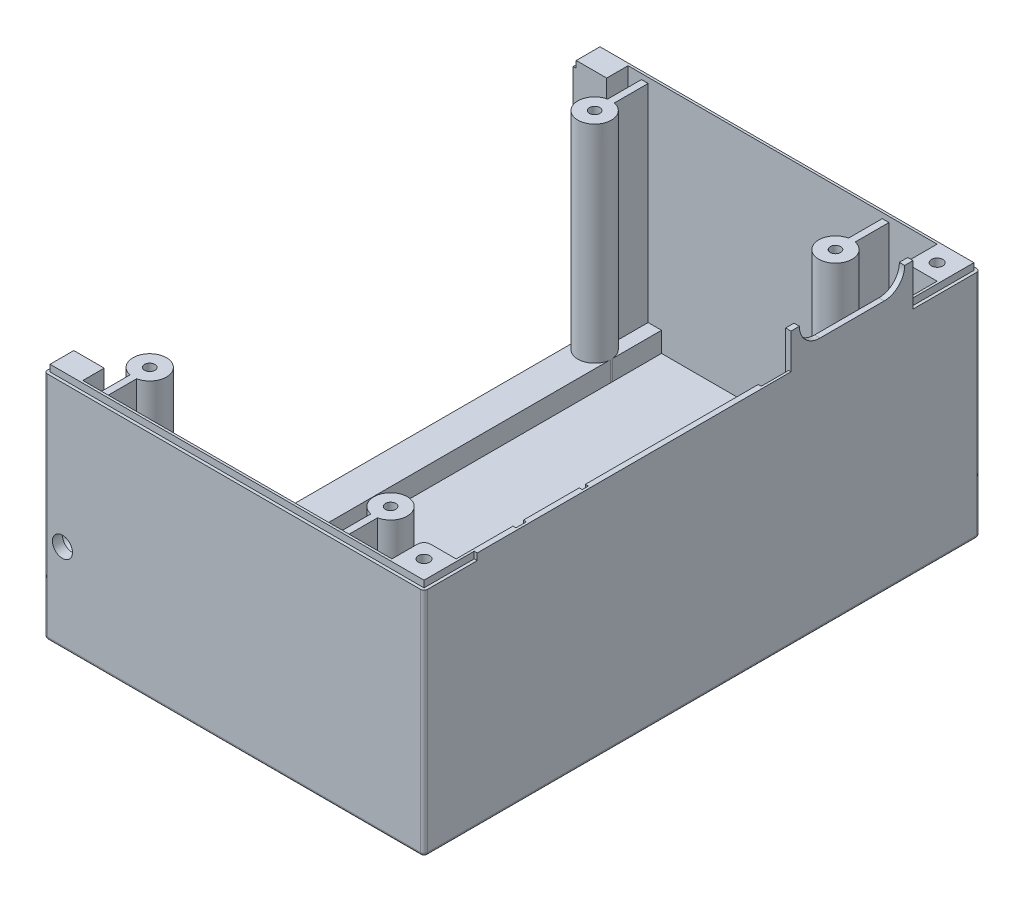
SolidWorks part; units mm, degrees
ref_plane "Спереди" through (0, 0, 0) normal (0, 0, 1) x (1, 0, 0)
ref_plane "Сверху" through (0, 0, 0) normal (0, 1, 0) x (1, 0, 0)
ref_plane "Справа" through (0, 0, 0) normal (1, 0, 0) x (0, 0, -1)
sketch "Эскиз1" plane through (0, 0, 0) normal (0, 1, 0) x (1, 0, 0)
  line L4 (54.2, -83.1) -> (54.2, 83.1)
  line L9 (-59.4, 83.1) -> (-59.4, -83.1)
  line L10 (-59.4, 83.1) -> (54.2, 83.1)
  line L11 (-59.4, -83.1) -> (54.2, -83.1)
  point P0 (0, 0)
extrude "Бобышка-Вытянуть1" add sketch "Эскиз1" against normal blind 1.6
sketch "Эскиз2" plane through (0, 0, 0) normal (0, 1, 0) x (1, 0, 0)
  line L0 (-54.2, 83.1) -> (54.2, 83.1)
  line L1 (54.2, 83.1) -> (54.2, -83.1)
  line L24 (52.6, -81.5) -> (52.6, 81.5)
  line L26 (-49.4, 75.1) -> (-49.4, 81.5)
  line L27 (-49.4, 81.5) -> (52.6, 81.5)
  line L29 (-49.4, -75.1) -> (-49.4, -81.5)
  line L30 (-49.4, -81.5) -> (52.6, -81.5)
  line L31 (-59.4, 75.1) -> (-59.4, 83.1)
  line L32 (-59.4, 83.1) -> (-59.4, -83.1) construction
  line L33 (-49.4, 75.1) -> (-59.4, 75.1)
  line L34 (-54.2, 83.1) -> (-59.4, 83.1)
  line L35 (-59.4, -75.1) -> (-59.4, -83.1)
  line L36 (-49.4, -75.1) -> (-59.4, -75.1)
  line L37 (-59.4, -83.1) -> (54.2, -83.1)
extrude "Бобышка-Вытянуть2" add sketch "Эскиз2" along normal blind 69.5
sketch "Эскиз3" plane through (0, 0, 0) normal (0, 1, 0) x (1, 0, 0)
  line L1 (22.6, 81.5) -> (32.6, 81.5)
  line L14 (-49.4, 81.5) -> (-39.4, 81.5)
  line L22 (-49.4, 81.5) -> (-49.4, -81.5)
  line L24 (-49.4, -81.5) -> (-39.4, -81.5)
  line L25 (-39.4, -81.5) -> (-39.4, 81.5)
  line L26 (22.6, 81.5) -> (22.6, -81.5)
  line L27 (32.6, 81.5) -> (32.6, -81.5)
  line L28 (32.6, -81.5) -> (22.6, -81.5)
extrude "Бобышка-Вытянуть3" add sketch "Эскиз3" along normal blind 6
sketch "Эскиз17" plane through (0, 6, 0) normal (0, 1, 0) x (1, 0, 0)
  circle A2 centre (27.1, 46.25) radius 1.55
  circle A3 centre (-42.9, -46.25) radius 1.55
sketch "Эскиз20" plane through (0, 0, 0) normal (0, 1, 0) x (1, 0, 0)
  circle A1 centre (-44.4, -66.5) radius 5
  circle A2 centre (-44.3902, 66.5) radius 5
  circle A3 centre (27.6, 66.5) radius 5
  circle A4 centre (27.6, -66.5) radius 5
extrude "Бобышка-Вытянуть7" add sketch "Эскиз20" along normal blind 67.9
sketch "Эскиз25" plane through (0, 0, 0) normal (0, 1, 0) x (1, 0, 0)
  line L0 (43, -71.9) -> (43, -81.5)
  line L1 (52.6, 81.5) -> (43, 81.5)
  line L2 (52.6, 81.5) -> (52.6, 71.9)
  line L3 (52.6, 71.9) -> (43, 71.9)
  line L4 (43, 81.5) -> (43, 71.9)
  line L7 (52.6, -71.9) -> (43, -71.9)
  line L10 (43, -81.5) -> (52.6, -81.5)
  line L11 (52.6, -81.5) -> (52.6, -71.9)
extrude "Бобышка-Вытянуть8" add sketch "Эскиз25" along normal blind 69.5
sketch "Эскиз26" plane through (0, 69.5, 0) normal (0, 1, 0) x (1, 0, 0)
  circle A0 centre (47.8, 76.7) radius 1.25
  circle A1 centre (47.8, 76.7) radius 2.8
  circle A2 centre (47.7909, -76.7) radius 1.25
  circle A3 centre (47.7909, -76.7) radius 2.8
sketch "Эскиз27" plane through (0, 67.9, 0) normal (0, 1, 0) x (1, 0, 0)
  circle A0 centre (-44.3902, 66.5) radius 1.55
  circle A1 centre (27.6, 66.5) radius 1.55
  circle A2 centre (27.6, -66.5) radius 1.55
  circle A3 centre (-44.4, -66.5) radius 1.55
extrude "Вырез-Вытянуть1" cut sketch "Эскиз27" against normal blind 6
sketch "Эскиз29" plane through (54.2, 0, 0) normal (1, 0, 0) x (0, 0, -1)
  line L2 (-83.1, 69.5) -> (83.1, 69.5) construction
  line L3 (35.3314, 73.9) -> (54.3686, 73.9)
  line L5 (26.6, 69.5) -> (63.1, 69.5)
  line L12 (26.6, 80.0414) -> (26.6, 69.5)
  line L15 (63.1, 80.0414) -> (63.1, 69.5)
  line L17 (26.6, 80.0414) -> (29.1, 80.0414)
  line L18 (63.1, 80.0414) -> (60.6, 80.0414)
  line L19 (54.4586, 73.9) -> (54.3686, 73.9)
  line L20 (35.2414, 73.9) -> (35.3314, 73.9)
  arc A4 (60.6, 80.0414) -> (54.4586, 73.9) centre (54.4586, 80.0414) cw
  arc A5 (29.1, 80.0414) -> (35.2414, 73.9) centre (35.2414, 80.0414) ccw
  dimension "D1" = 10.5414
  dimension "D3" = 2.5
extrude "Бобышка-Вытянуть9" add sketch "Эскиз29" against normal blind 1.6
sketch "Эскиз30" plane through (0, -1.6, 0) normal (0, -1, 0) x (1, 0, 0)
  circle A1 centre (47.8, -76.7) radius 3.2
extrude "Вырез-Вытянуть2" cut sketch "Эскиз30" against normal blind 65.5
sketch "Эскиз31" plane through (0, 63.9, 0) normal (0, -1, 0) x (1, 0, 0)
  circle A0 centre (47.8, -76.7) radius 2.8
sketch "Эскиз36" plane through (0, 69.5, 0) normal (0, 1, 0) x (1, 0, 0)
  line L4 (54.2, -82.4) -> (54.2, -83.1)
  line L5 (54.2, -83.1) -> (-54.2, -83.1)
  line L12 (-54.2, 83.1) -> (54.2, 83.1)
  line L33 (54.2, 83.1) -> (54.2, 63.1)
  line L38 (53.3, 82.2) -> (53.3, 63.1)
  line L39 (-59.4, 83.1) -> (-59.4, 75.1)
  line L42 (53.3, -82.2002) -> (53.3, -67.2)
  line L43 (53.3, -67.2) -> (54.2, -67.2)
  line L50 (54.2, -67.2) -> (54.2, -82.4)
  line L54 (53.3, -82.2002) -> (-52.6, -82.2002)
  line L57 (54.2, 63.1) -> (53.3, 63.1)
  line L58 (52.6, 63.1) -> (54.2, 63.1) construction
  line L59 (-59.4, 75.1) -> (-58.5, 75.1)
  line L60 (-59.4, 75.1) -> (-49.4, 75.1) construction
  line L61 (-58.5, 75.1) -> (-58.5, 82.2)
  line L62 (-59.4, 83.1) -> (-54.2, 83.1)
  line L63 (-58.5, 82.2) -> (53.3, 82.2)
  line L64 (-59.4, -83.1) -> (-59.4, -75.1)
  line L65 (-59.4, -75.1) -> (-58.5, -75.1)
  line L66 (-49.4, -75.1) -> (-59.4, -75.1) construction
  line L67 (-58.5, -75.1) -> (-58.5, -82.2002)
  line L68 (-58.5, -82.2002) -> (-52.6, -82.2002)
  line L69 (-59.4, -83.1) -> (-54.2, -83.1)
sketch "Эскиз38" plane through (0, 69.5, 0) normal (0, 1, 0) x (1, 0, 0)
  circle A0 centre (47.8, 76.7) radius 1.7
  dimension "D1" = 3.4
extrude "Вырез-Вытянуть9" cut sketch "Эскиз38" against normal blind 3.9 contours A0
loft "Вырез-По сечениям1" cut profiles "Эскиз31" section edge at (47.8, 65.6, -75) section "Эскиз31"
pattern_linear "Линейный массив3" count 2 spacing 153.4 along (0, 0, 1) of "Вырез-Вытянуть2", "Вырез-Вытянуть9", "Вырез-По сечениям1"
extrude "Вырез-Вытянуть8" cut sketch "Эскиз36" against normal blind 2
sketch "Эскиз50" plane through (0, 69.5, 0) normal (0, 1, 0) x (1, 0, 0)
  line L0 (52.6, 26.6) -> (53.5, 26.6)
  line L1 (53.5, 26.6) -> (53.5, 18.425)
  line L2 (53.5, 18.425) -> (52.6, 18.425)
  line L3 (52.6, 18.425) -> (52.6, 26.6)
  line L4 (52.6, -33.275) -> (53.5, -33.275)
  line L5 (53.5, -33.275) -> (53.5, -35.1)
  line L6 (53.5, -35.1) -> (52.6, -35.1)
  line L7 (52.6, -35.1) -> (52.6, -33.275)
  line L8 (52.6, -51.8) -> (53.5, -51.8)
  line L9 (53.5, -51.8) -> (53.5, -54.9)
  line L10 (53.5, -54.9) -> (52.6, -54.9)
  line L11 (52.6, -54.9) -> (52.6, -51.8)
extrude "Вырез-Вытянуть14" cut sketch "Эскиз50" against normal blind 2
sketch "Эскиз40" plane through (0, 0, 0) normal (0, 1, 0) x (1, 0, 0)
  line L2 (-54.2, -75.1) -> (-54.2, 75.1)
  line L6 (-54.2, 75.1) -> (-59.4, 75.1)
  line L7 (-59.4, 75.1) -> (-59.4, -75.1)
  line L9 (-59.4, -75.1) -> (-54.2, -75.1)
extrude "Вырез-Вытянуть10" cut sketch "Эскиз40" against normal blind 1.6
sketch "Эскиз42" plane through (0, 0, 83.1) normal (0, 0, 1) x (1, 0, 0)
  circle A1 centre (-53.9, 25) radius 3
sketch "Эскиз47" plane through (0, 0, 83.1) normal (0, 0, 1) x (1, 0, 0)
  point P0 (-53.9, 25)
hole_wizard "Отверстие1" positions "Эскиз47" profile "Эскиз48" legacy
sketch "Эскиз48" plane through (-53.9, 25, 83.1) normal (1, 0, 0) x (0, -1, 0)
  line L0 (0, 0) -> (0, 9)
  line L1 (0, 9) -> (1.55, 8.0687)
  line L2 (1.55, 8.0687) -> (1.55, 4.45)
  line L3 (1.55, 4.45) -> (3, 3)
  line L4 (3, 3) -> (3, 0)
  line L5 (3, 0) -> (0, 0)
  line L6 (0, -6.13) -> (0, 109.2824) construction
  line L7 (-1.55, 4.45) -> (-3, 3) construction
  line L8 (0, 9) -> (-1.55, 8.0687) construction
  dimension "Диаметр" = 3.1
  dimension "Глубина" = 9
  dimension "Диаметр рассверливания" = 6
  dimension "Глубина рассверливания" = 3
  dimension "Угол заточки сверла" = 118
  dimension "Угол рассверл." = 90
mirror "Зеркальное отражение5" about plane through (0, 0, 0) normal (0, 0, 1) of "Отверстие1"
fillet "Скругление2" radius 2 2 edges at (43, 34.75, -71.9) (43, 34.75, 71.9)
fillet "Скругление3" radius 1 4 edges at (-59.4, 32.95, -83.1) (54.2, 32.95, -83.1) (54.2, 32.95, 83.1) (-59.4, 32.95, 83.1)
sketch "Эскиз46" plane through (0, 6, 0) normal (0, 1, 0) x (1, 0, 0)
  line L3 (-45.4, 81.5) -> (-45.4, 71.397)
  line L5 (-43.4, 81.5) -> (-43.4, 71.401)
  line L6 (-45.4, 71.397) -> (-43.4, 71.401)
  line L10 (-45.4, 81.5) -> (-43.4, 81.5)
  circle A0 centre (-44.3902, 66.5) radius 5 construction
  arc A1 (-39.4, 66.8135) -> (-39.4, 66.1865) centre (-44.3902, 66.5) ccw construction
extrude "Бобышка-Вытянуть13" add sketch "Эскиз46" along normal blind 61.9
mirror "Зеркальное отражение4" about plane through (0, 0, 0) normal (0, 0, 1) of "Бобышка-Вытянуть13"
pattern_linear "Линейный массив4" count 2 spacing 72 along (1, 0, 0) of "Зеркальное отражение4", "Бобышка-Вытянуть13"
extrude "Вырез-Вытянуть13" cut sketch "Эскиз17" against normal blind 6
fillet "Скругление4" radius 1 9 edges at (54.2, -1.6, 0) (-59.4, -1.6, 78.6) (-59.1071, -1.6, 82.8071) (-2.6, -1.6, 83.1) (53.9071, -1.6, 82.8071) (-59.4, -1.6, -78.6) (-59.1071, -1.6, -82.8071) (-2.6, -1.6, -83.1) (53.9071, -1.6, -82.8071)
